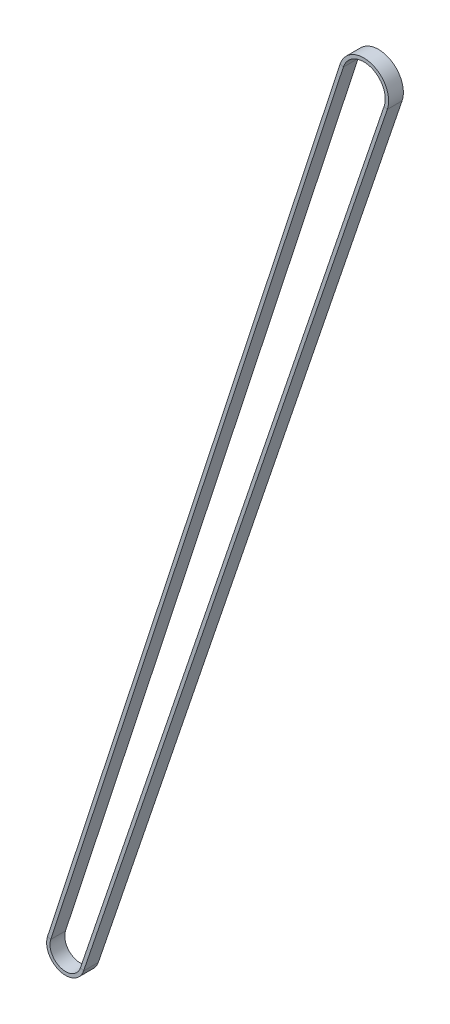
SolidWorks part; units mm, degrees
material "BUTYL"
ref_plane "Front Plane" through (0, 0, 0) normal (0, 0, 1) x (1, 0, 0)
ref_plane "Top Plane" through (0, 0, 0) normal (0, 1, 0) x (1, 0, 0)
ref_plane "Right Plane" through (0, 0, 0) normal (1, 0, 0) x (0, 0, -1)
sketch "Sketch1" plane through (0, 0, 0) normal (0, 0, 1) x (1, 0, 0)
  line L0 (6.0152, -2.0346) -> (129.6722, 363.5599)
  line L1 (-6.0401, 1.9596) -> (113.0606, 369.0636)
  circle A0 centre (0, 0) radius 6.35 construction
  arc A1 (-6.0401, 1.9596) -> (6.0152, -2.0346) centre (0, 0) ccw
  circle A2 centre (121.3835, 366.3634) radius 8.75 construction
  arc A3 (129.6722, 363.5599) -> (113.0606, 369.0636) centre (121.3835, 366.3634) ccw
ref_plane "Plane1" through (113.0606, 369.0636, 0) normal (0.3086, 0.9512, 0) x (0.9512, -0.3086, 0)
sketch "Sketch2" plane through (113.0606, 369.0636, 0) normal (0.3086, 0.9512, 0) x (0.9512, -0.3086, 0)
  line L0 (-1.38, -3) -> (0, -3)
  line L1 (-1.38, -3) -> (-1.38, 3)
  line L2 (0, -3) -> (0, 3)
  line L3 (-1.38, 3) -> (0, 3)
  line L4 (-1.38, -3) -> (0, 3) construction
  line L5 (0, -3) -> (-1.38, 3) construction
  point P1 (-0.69, 0)
  point P2 (0, 0)
  dimension "D1" = 6
  dimension "D2" = 1.38
sweep "Sweep1" add profiles "Sketch2" path "Sketch1"
